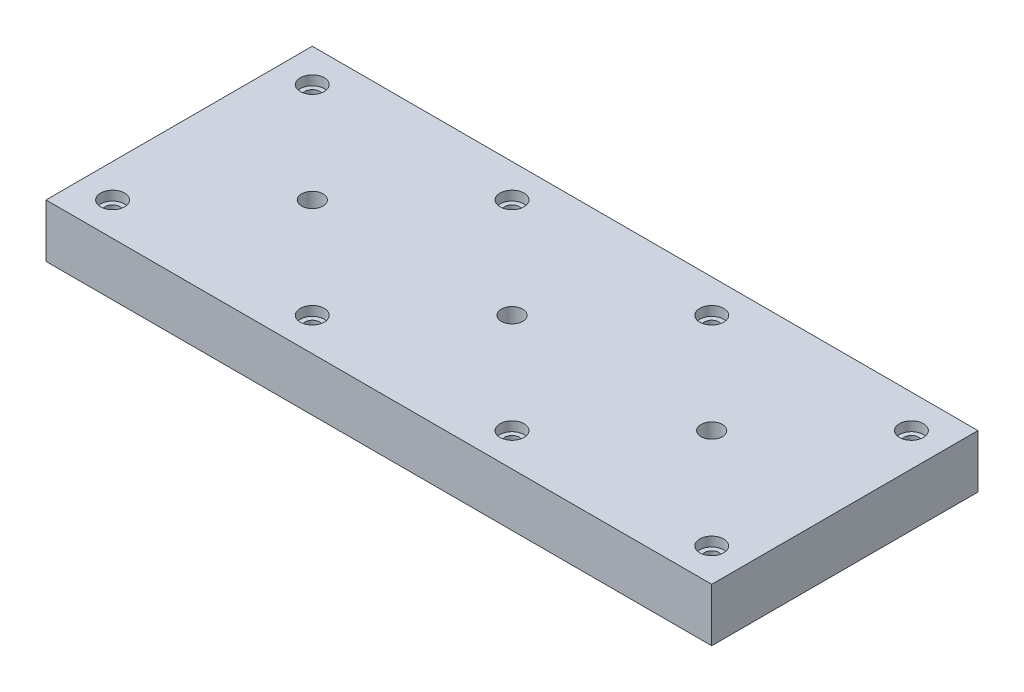
SolidWorks part; units mm, degrees
material "Liga 6061"
ref_plane "Plano frontal" through (0, 0, 0) normal (0, 0, 1) x (1, 0, 0)
ref_plane "Plano superior" through (0, 0, 0) normal (0, 1, 0) x (1, 0, 0)
ref_plane "Plano direito" through (0, 0, 0) normal (1, 0, 0) x (0, 0, -1)
sketch "Esboço1" plane through (0, 0, 0) normal (0, 1, 0) x (1, 0, 0)
  line L1 (-250, -100) -> (250, -100)
  line L2 (-250, -100) -> (-250, 100)
  line L3 (-250, 100) -> (250, 100)
  line L4 (250, -100) -> (250, 100)
  line L5 (-250, -100) -> (250, 100) construction
  line L6 (-250, 100) -> (250, -100) construction
  point P0 (0, 0)
  dimension "D1" = 500
  dimension "D2" = 200
extrude "Ressalto-extrusão1" add sketch "Esboço1" along normal blind 40
hole_wizard "Rebaixo para parafuso Allen sextavado de M101" positions "Esboço3" profile "Esboço2" counterbore size "M10" standard "DIN" end condition up to next
sketch "Esboço3" plane through (0, 40, 0) normal (0, 1, 0) x (1, 0, 0)
  line L0 (-250, 100) -> (-250, -100) construction
  line L1 (250, 100) -> (-250, 100) construction
  point P0 (-225, 75)
  point P12 (-75, 75)
  point P13 (75, 75)
  point P21 (-75, -75)
  point P22 (75, -75)
  point P30 (-225, -75)
  point P31 (225, 75)
  point P32 (225, -75)
  dimension "D1" = 25
  dimension "D2" = 25
  dimension "D3" = 4
  dimension "D4" = 2
sketch "Esboço2" plane through (-225, 40, -75) normal (1, 0, 0) x (0, 0, 1)
  line L0 (0, 0) -> (0, 40)
  line L1 (0, 40) -> (5.5, 40)
  line L3 (5.5, 40) -> (5.5, 7.1)
  line L4 (5.5, 7.1) -> (9, 7.1)
  line L5 (9, 7.1) -> (9, 0)
  line L7 (9, 0) -> (0, 0)
  line L11 (0, -6.35) -> (0, 107.95) construction
  dimension "Thru Hole Dia." = 11
  dimension "Thru Hole Depth" = 40
  dimension "C'Bore Dia." = 18
  dimension "C'Bore Depth" = 7.1
hole_wizard "Furo roscado de M18x2.0" positions "Esboço7" profile "Esboço6" tap size "M18x2.0" standard "Ansi Metric" end condition up to next
sketch "Esboço7" plane through (0, 40, 0) normal (0, 1, 0) x (1, 0, 0)
  line L0 (-250, 100) -> (-250, -100) construction
  line L1 (-150, 0) -> (-250, 0) construction
  point P0 (-150, 0)
  point P5 (-250, 0)
  point P72 (0, 0)
  point P73 (150, 0)
  dimension "D2" = 100
  dimension "D1" = 3
sketch "Esboço6" plane through (-150, 40, 0) normal (1, 0, 0) x (0, 0, 1)
  line L0 (0, 0) -> (0, 40)
  line L1 (0, 40) -> (8, 40)
  line L2 (8, 40) -> (8, 0)
  line L5 (8, 0) -> (0, 0)
  line L11 (0, -6.35) -> (0, 107.95) construction
  dimension "Thru Tap Drill Dia." = 16
  dimension "Thru Tap Drill Depth" = 40
cosmetic thread "Rosca de furo18"
cosmetic thread "Rosca de furo37"
cosmetic thread "Rosca de furo38"
hole_wizard "Furo roscado de M16x2.0" [suppressed] positions "Esboço9" profile "Esboço8" tap size "M16x2.0" standard "Ansi Metric"
sketch "Esboço9" plane through (0, 40, 0) normal (0, 1, 0) x (1, 0, 0)
  line L0 (-1020, 0) -> (-1050, 0) construction
  line L1 (-1050, 100) -> (-1050, -100) construction
  line L2 (1020, 0) -> (1050, 0) construction
  line L3 (1050, -100) -> (1050, 100) construction
  point P0 (-1020, 0)
  point P13 (-900, 0)
  point P14 (-780, 0)
  point P15 (-660, 0)
  point P16 (-540, 0)
  point P17 (-420, 0)
  point P18 (-300, 0)
  point P19 (-180, 0)
  point P20 (-60, 0)
  point P21 (60, 0)
  point P22 (180, 0)
  point P23 (300, 0)
  point P24 (420, 0)
  point P25 (540, 0)
  point P26 (660, 0)
  point P27 (780, 0)
  point P28 (900, 0)
  point P29 (1020, 0)
  dimension "D1" = 18
sketch "Esboço8" plane through (-1020, 40, 0) normal (1, 0, 0) x (0, 0, 1)
  line L0 (0, 0) -> (0, 40)
  line L1 (0, 40) -> (7, 40)
  line L2 (7, 40) -> (7, 0)
  line L5 (7, 0) -> (0, 0)
  line L11 (0, -6.35) -> (0, 107.95) construction
  dimension "Thru Tap Drill Dia." = 14
  dimension "Thru Tap Drill Depth" = 40
cosmetic thread "Rosca de furo19" [suppressed] parameters "D2"=16
cosmetic thread "Rosca de furo20" [suppressed] parameters "D2"=16
cosmetic thread "Rosca de furo21" [suppressed] parameters "D2"=16
cosmetic thread "Rosca de furo22" [suppressed] parameters "D2"=16
cosmetic thread "Rosca de furo23" [suppressed] parameters "D2"=16
cosmetic thread "Rosca de furo24" [suppressed] parameters "D2"=16
cosmetic thread "Rosca de furo25" [suppressed] parameters "D2"=16
cosmetic thread "Rosca de furo26" [suppressed] parameters "D2"=16
cosmetic thread "Rosca de furo27" [suppressed] parameters "D2"=16
cosmetic thread "Rosca de furo28" [suppressed] parameters "D2"=16
cosmetic thread "Rosca de furo29" [suppressed] parameters "D2"=16
cosmetic thread "Rosca de furo30" [suppressed] parameters "D2"=16
cosmetic thread "Rosca de furo31" [suppressed] parameters "D2"=16
cosmetic thread "Rosca de furo32" [suppressed] parameters "D2"=16
cosmetic thread "Rosca de furo33" [suppressed] parameters "D2"=16
cosmetic thread "Rosca de furo34" [suppressed] parameters "D2"=16
cosmetic thread "Rosca de furo35" [suppressed] parameters "D2"=16
cosmetic thread "Rosca de furo36" [suppressed] parameters "D2"=16
